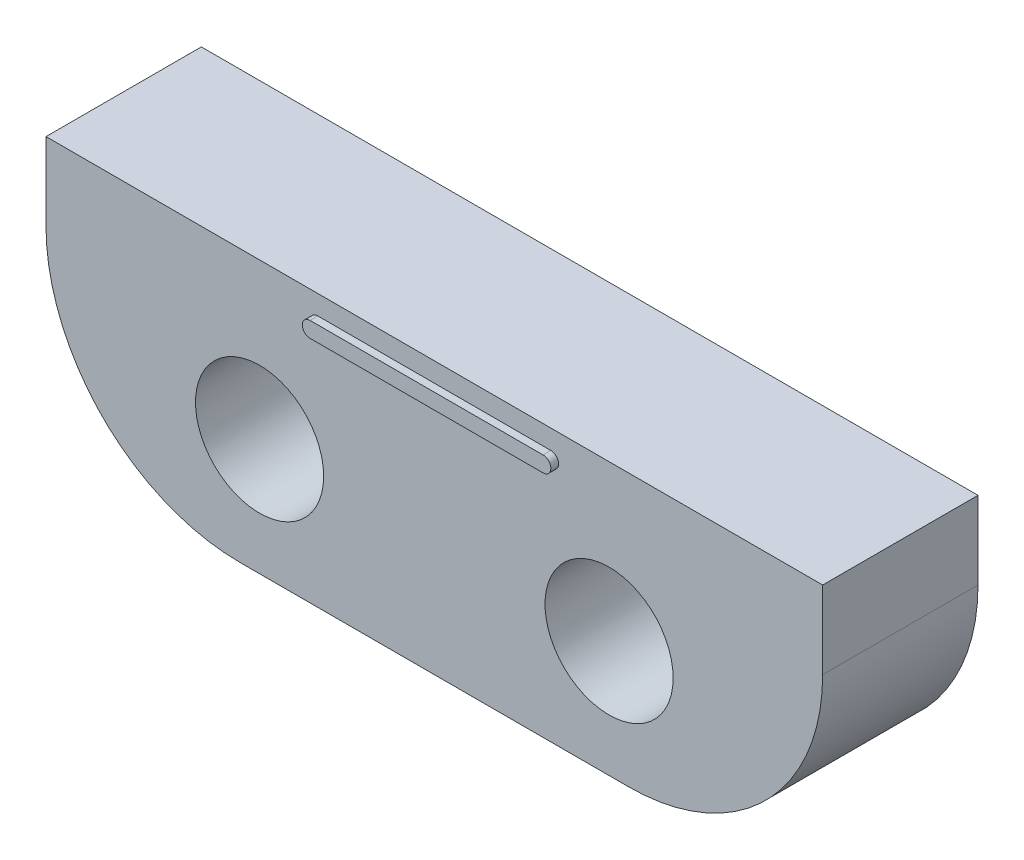
SolidWorks part; units mm, degrees
ref_plane "Front Plane" through (0, 0, 0) normal (0, 0, 1) x (1, 0, 0)
ref_plane "Top Plane" through (0, 0, 0) normal (0, 1, 0) x (1, 0, 0)
ref_plane "Right Plane" through (0, 0, 0) normal (1, 0, 0) x (0, 0, -1)
sketch "Sketch1" plane through (0, 0, 0) normal (0, 0, 1) x (1, 0, 0)
  line L0 (4.5, 0) -> (-4.5, 0) construction
  line L2 (-10, 4) -> (10, 4)
  line L3 (-10, 4) -> (-10, -3)
  line L4 (-10, -3) -> (10, -3)
  line L5 (10, 4) -> (10, -3)
  circle A0 centre (-4.5, 0) radius 1.65
  circle A1 centre (4.5, 0) radius 1.65
  point P4 (0, 0)
  point P10 (0, 4)
  point P11 (0, -2.6059)
  point P12 (0, 0)
  point P13 (10, 0.5)
  dimension "D2" = 3.3
  dimension "D1" = 9
  dimension "D3" = 4
  dimension "D4" = 20
  dimension "D5" = 3
extrude "Boss-Extrude1" add sketch "Sketch1" along normal blind 4
sketch "Sketch2" plane through (0, 0, 4) normal (0, 0, 1) x (1, 0, 0)
  line L0 (-3, 3.5) -> (3, 3.5)
  line L1 (3, 3.1) -> (-3, 3.1)
  line L2 (10, 4) -> (-10, 4) construction
  arc A0 (3, 3.5) -> (3, 3.1) centre (3, 3.3) cw
  arc A1 (-3, 3.1) -> (-3, 3.5) centre (-3, 3.3) cw
  point P6 (0, 3.5)
  point P10 (-4.3384, 3.3)
  dimension "D1" = 0.4
  dimension "D2" = 0.9
  dimension "D3" = 6
extrude "Boss-Extrude2" add sketch "Sketch2" along normal blind 0.2
fillet "Fillet1" radius 5 2 edges at (-10, -3, 2) (10, -3, 2)
